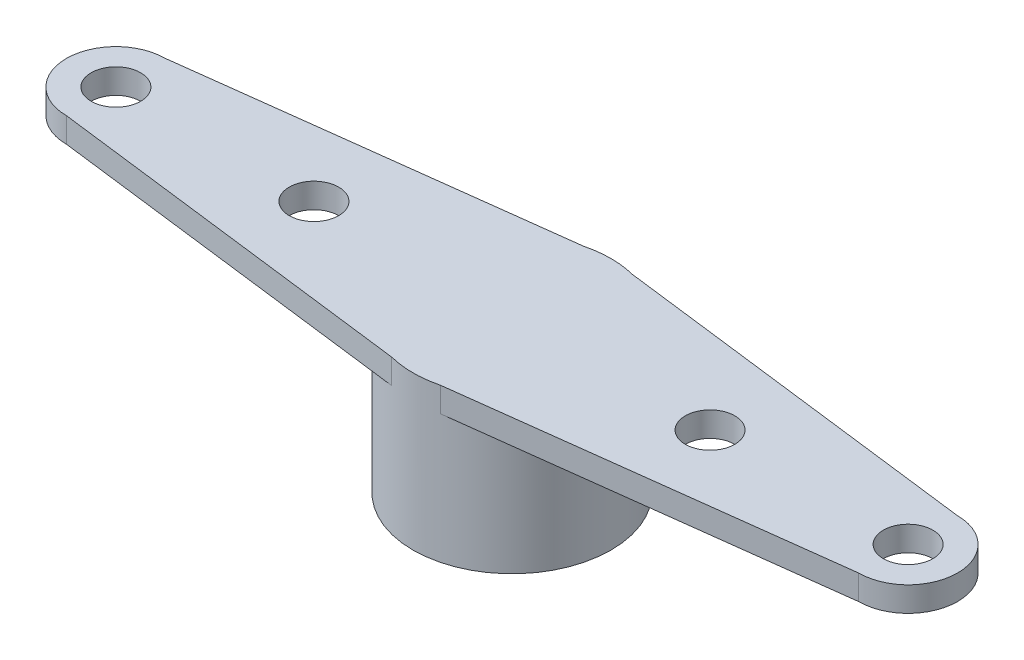
SolidWorks part; units mm, degrees
ref_plane "Front Plane" through (0, 0, 0) normal (0, 0, 1) x (1, 0, 0)
ref_plane "Top Plane" through (0, 0, 0) normal (0, 1, 0) x (1, 0, 0)
ref_plane "Right Plane" through (0, 0, 0) normal (1, 0, 0) x (0, 0, -1)
sketch "Sketch2" plane through (0, 0, 0) normal (0, 1, 0) x (1, 0, 0)
  line L1 (-10.16, -1.27) -> (-0.6252, -2.4618)
  line L2 (10.16, 1.27) -> (0.6252, 2.4618)
  line L3 (10.16, -1.27) -> (0.6252, -2.4618)
  line L4 (-10.16, 1.27) -> (-0.6252, 2.4618)
  arc A0 (0.6252, 2.4618) -> (-0.6252, 2.4618) centre (0, 0) ccw
  arc A1 (10.16, -1.27) -> (10.16, 1.27) centre (10.16, 0) ccw
  circle A2 centre (5.08, 0) radius 0.635
  circle A3 centre (10.16, 0) radius 0.635
  arc A4 (-10.16, -1.27) -> (-10.16, 1.27) centre (-10.16, 0) cw
  circle A5 centre (-10.16, 0) radius 0.635
  circle A6 centre (-5.08, 0) radius 0.635
  arc A7 (-0.6252, -2.4618) -> (0.6252, -2.4618) centre (0, 0) ccw
extrude "Boss-Extrude2" add sketch "Sketch2" along normal blind 0.635
sketch "Sketch3" plane through (0, 0, 0) normal (0, -1, 0) x (1, 0, 0)
  circle A0 centre (0, 0) radius 2.54
extrude "Boss-Extrude3" add sketch "Sketch3" along normal blind 3.302
sketch "Sketch4" plane through (0, -3.302, 0) normal (0, -1, 0) x (-1, 0, 0)
  circle A0 centre (0, 0) radius 2.286
extrude "Cut-Extrude1" cut sketch "Sketch4" against normal blind 3.302
